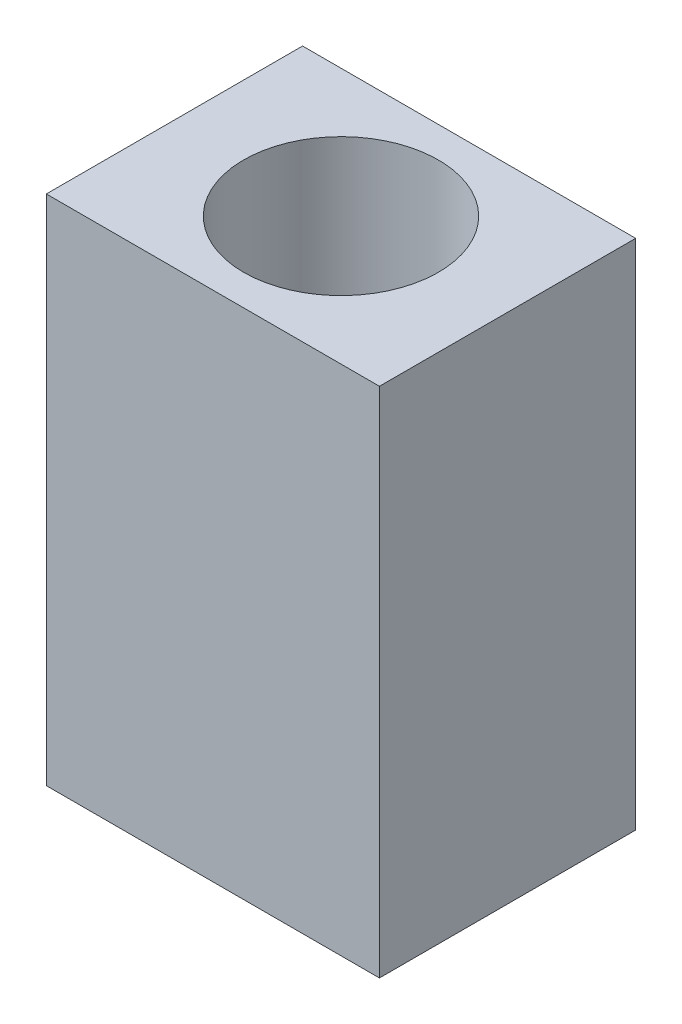
SolidWorks part; units mm, degrees
ref_plane "Front Plane" through (0, 0, 0) normal (0, 0, 1) x (1, 0, 0)
ref_plane "Top Plane" through (0, 0, 0) normal (0, 1, 0) x (1, 0, 0)
ref_plane "Right Plane" through (0, 0, 0) normal (1, 0, 0) x (0, 0, -1)
sketch "Sketch3" plane through (0, 0, 0) normal (0, 0, 1) x (1, 0, 0)
  line L0 (0, 0) -> (13, 0)
  line L1 (0, 0) -> (0, 20)
  line L2 (13, 0) -> (13, 20)
  line L3 (0, 20) -> (13, 20)
extrude "Boss-Extrude1" add sketch "Sketch3" along normal blind 10
sketch "Sketch4" plane through (0, 20, 0) normal (0, 1, 0) x (1, 0, 0)
  circle A0 centre (6.5, -5) radius 3.8
  point P2 (6.5, -5)
  point P5 (0, -5)
extrude "Cut-Extrude1" cut sketch "Sketch4" against normal blind 17
sketch "Sketch5" plane through (0, 0, 0) normal (0, 0, -1) x (-1, 0, 0)
  line L1 (-6.5, 40) -> (-6.5, 0)
  line L3 (0, 0) -> (-13, 0) construction
  line L4 (13, 10) -> (-13, 10)
  line L6 (-13, 0) -> (-13, 20) construction
  point P2 (-2.7, 12.8925)
  point P9 (-6.5, 20)
  point P10 (0, 10)
  point P21 (-2.6106, 13.166)
  point P22 (-2.7, 7.5034)
  point P25 (-10.3, 13.166)
  point P28 (-10.3, 7.5034)
